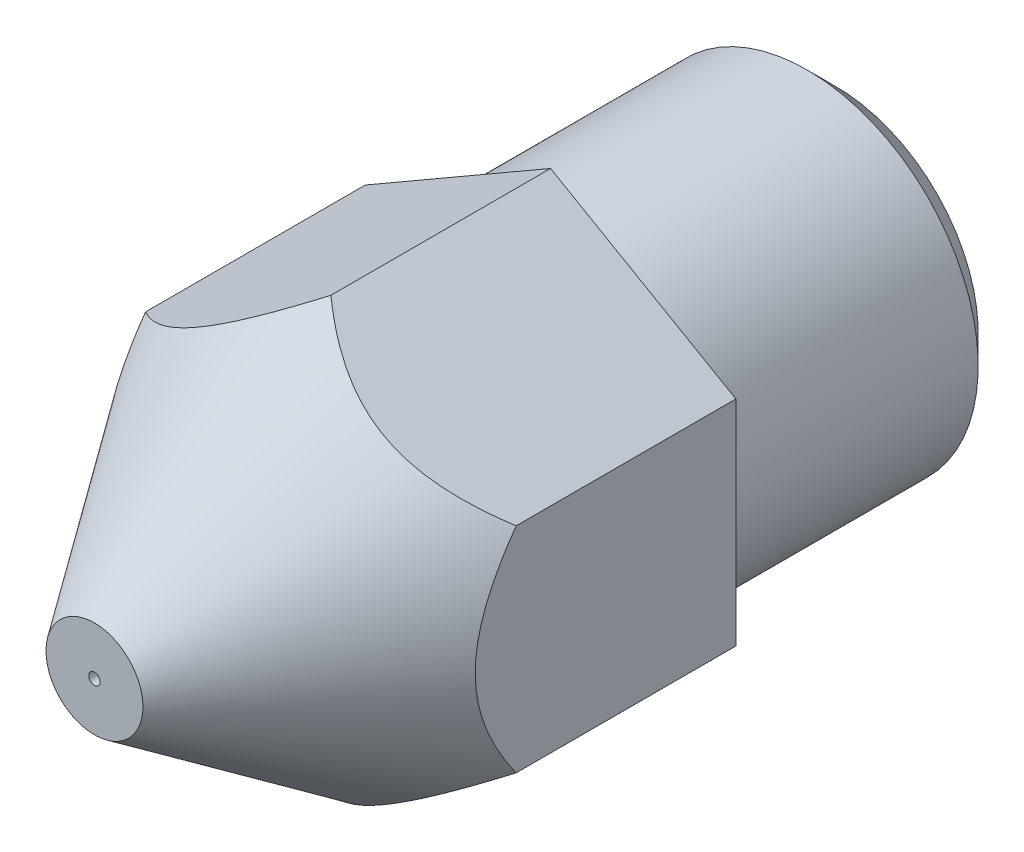
SolidWorks part; units mm, degrees
material "Brass"
ref_plane "Front Plane" through (0, 0, 0) normal (0, 0, 1) x (1, 0, 0)
ref_plane "Top Plane" through (0, 0, 0) normal (0, 1, 0) x (1, 0, 0)
ref_plane "Right Plane" through (0, 0, 0) normal (1, 0, 0) x (0, 0, -1)
sketch "Sketch1" plane through (0, 0, 0) normal (0, 1, 0) x (1, 0, 0)
  line L0 (0, 0) -> (0, -50000) construction
  line L1 (0, 0) -> (-50000, 0) construction
  line L2 (1, 8.5) -> (3, 8.5)
  line L3 (0.85, -4.5) -> (4, 0)
  line L4 (4, 0) -> (4, 3.5)
  line L5 (0, -4.5) -> (0, -3.5)
  line L10 (1, 8.5) -> (1, -1.7679)
  line L14 (3, 8.5) -> (3, 3.5)
  line L20 (0, -3.5) -> (1, -1.7679)
  line L23 (3, 3.5) -> (4, 3.5)
  line L24 (0, -4.5) -> (0.85, -4.5)
  line L25 (4, 0) -> (50001.5, 0) construction
  dimension "D1" = 1
  dimension "D2" = 3
  dimension "D3" = 3.5
  dimension "D4" = 1.7
  dimension "D5" = 1
  dimension "D6" = 13
  dimension "D7" = 5
  dimension "D9" = 4
  dimension "D11" = 30
ref_axis "Axis1" through (0, 0, 0) along (0, 0, 1)
revolve "Revolve1" add sketch "Sketch1" angle 360 about axis through (0, 0, 0) along (0, 0, 1)
sketch "Sketch2" plane through (0, 0, -3.5) normal (0, 0, -1) x (-1, 0, 0)
  line L0 (0, 0) -> (0, 50000) construction
  line L1 (0, 0) -> (50000, 0) construction
  line L2 (3.25, 1.8764) -> (0, 3.7528)
  line L3 (3.25, 1.8764) -> (3.25, -1.8764)
  line L4 (3.25, -1.8764) -> (0, -3.7528)
  line L5 (0, 0) -> (43301.2702, 25000) construction
  line L6 (0, 0) -> (43062.4912, -24862.1409) construction
  line L7 (-3.25, 1.8764) -> (0, 3.7528)
  line L8 (-3.25, 1.8764) -> (-3.25, -1.8764)
  line L9 (-3.25, -1.8764) -> (0, -3.7528)
  circle A1 centre (0, 0) radius 11.8883
  dimension "D1" = 60
  dimension "D2" = 30
  dimension "D3" = 3.25
extrude "Cut-Extrude2" cut sketch "Sketch2" against normal blind 10
chamfer "Chamfer1" distance 0.5 angle 45 1 edges at (-3, 0, -8.5)
sketch "Sketch3" plane through (0, 0, 4.5) normal (0, 0, 1) x (1, 0, 0)
  circle A0 centre (0, 0) radius 0.1
  dimension "D1" = 0.2
extrude "Cut-Extrude3" cut sketch "Sketch3" against normal through all
